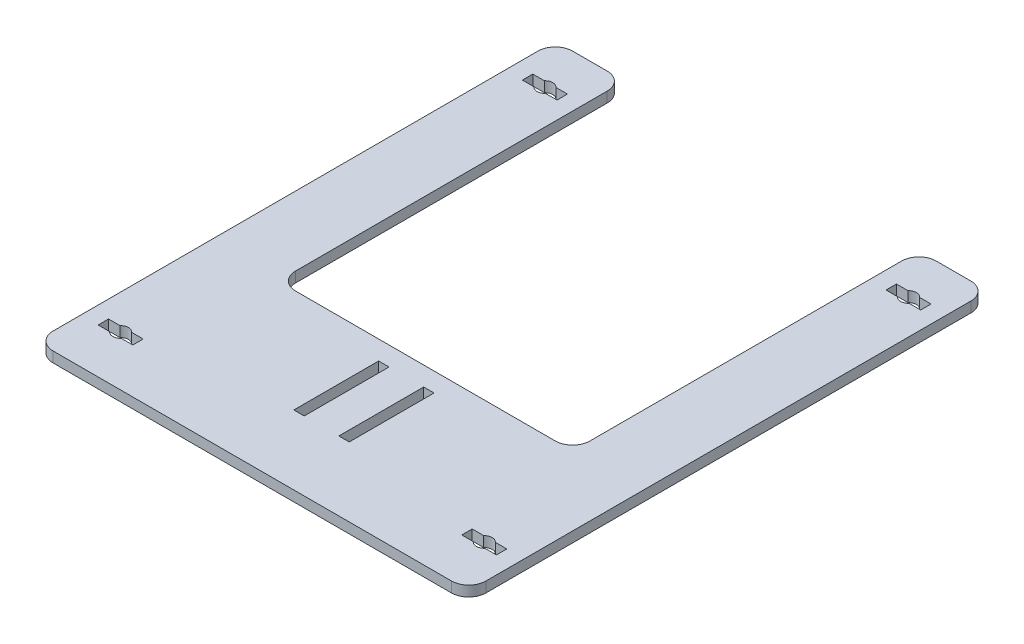
SolidWorks part; units mm, degrees
ref_plane "Front Plane" through (0, 0, 0) normal (0, 0, 1) x (1, 0, 0)
ref_plane "Top Plane" through (0, 0, 0) normal (0, 1, 0) x (1, 0, 0)
ref_plane "Right Plane" through (0, 0, 0) normal (1, 0, 0) x (0, 0, -1)
sketch "Sketch1" plane through (0, 0, 0) normal (0, 1, 0) x (1, 0, 0)
  line L0 (-164.1155, 87.3804) -> (-124.1155, 87.3804)
  line L1 (-124.1155, 87.3804) -> (-124.1155, -112.6196)
  line L2 (-124.1155, -112.6196) -> (45.8845, -112.6196)
  line L3 (45.8845, -112.6196) -> (45.8845, 87.3804)
  line L4 (45.8845, 87.3804) -> (85.8845, 87.3804)
  line L5 (85.8845, 87.3804) -> (85.8845, -212.6196)
  line L6 (85.8845, -212.6196) -> (-164.1155, -212.6196)
  line L7 (-164.1155, -212.6196) -> (-164.1155, 87.3804)
  dimension "D1" = 300
  dimension "D2" = 40
  dimension "D3" = 40
  dimension "D4" = 90
  dimension "D5" = 300
  dimension "D6" = 250
  dimension "D7" = 250
  dimension "D8" = 100
extrude "Boss-Extrude1" add sketch "Sketch1" along normal blind 6
fillet "Fillet1" radius 10 8 edges at (-164.1155, 3, -87.3804) (-124.1155, 3, -87.3804) (-124.1155, 3, 112.6196) (45.8845, 3, 112.6196) (45.8845, 3, -87.3804) (85.8845, 3, -87.3804) (85.8845, 3, 212.6196) (-164.1155, 3, 212.6196)
sketch "Sketch2" plane through (0, 0, 0) normal (0, -1, 0) x (1, 0, 0)
  line L0 (-55.1155, 172.6196) -> (-49.1155, 172.6196) construction
  line L1 (-29.1155, 172.6196) -> (-23.1155, 172.6196) construction
  line L2 (-55.1155, 172.6196) -> (-49.1155, 172.6196)
  line L3 (-29.1155, 172.6196) -> (-23.1155, 172.6196)
  line L4 (-55.1155, 172.6196) -> (-55.1155, 123.6196)
  line L5 (-55.1155, 123.6196) -> (-49.1155, 123.6196)
  line L6 (-49.1155, 277.6196) -> (-49.1155, -2.3804) construction
  line L7 (-49.1155, 123.6196) -> (-49.1155, 172.6196)
  line L8 (-164.1155, 202.6196) -> (-164.1155, -77.3804)
  line L9 (-154.1155, -87.3804) -> (-134.1155, -87.3804)
  line L10 (-124.1155, -77.3804) -> (-124.1155, 102.6196)
  line L11 (-114.1155, 112.6196) -> (35.8845, 112.6196)
  line L12 (45.8845, 102.6196) -> (45.8845, -77.3804)
  line L13 (55.8845, -87.3804) -> (75.8845, -87.3804)
  line L14 (85.8845, -77.3804) -> (85.8845, 202.6196)
  line L15 (75.8845, 212.6196) -> (-154.1155, 212.6196)
  line L16 (-164.1155, 202.6196) -> (-164.1155, -77.3804)
  line L17 (-154.1155, -87.3804) -> (-134.1155, -87.3804)
  line L18 (-124.1155, -77.3804) -> (-124.1155, 102.6196)
  line L19 (-114.1155, 112.6196) -> (35.8845, 112.6196)
  line L20 (45.8845, 102.6196) -> (45.8845, -77.3804)
  line L21 (55.8845, -87.3804) -> (75.8845, -87.3804)
  line L22 (85.8845, -77.3804) -> (85.8845, 202.6196)
  line L23 (75.8845, 212.6196) -> (-154.1155, 212.6196)
  line L24 (-29.1155, 172.6196) -> (-29.1155, 123.6196)
  line L25 (-29.1155, 123.6196) -> (-23.1155, 123.6196)
  line L26 (-23.1155, 277.6196) -> (-23.1155, -2.3804) construction
  line L27 (-23.1155, 123.6196) -> (-23.1155, 172.6196)
  arc A8 (-164.1155, -77.3804) -> (-154.1155, -87.3804) centre (-154.1155, -77.3804) ccw
  arc A9 (-134.1155, -87.3804) -> (-124.1155, -77.3804) centre (-134.1155, -77.3804) ccw
  arc A10 (-114.1155, 112.6196) -> (-124.1155, 102.6196) centre (-114.1155, 102.6196) ccw
  arc A11 (45.8845, 102.6196) -> (35.8845, 112.6196) centre (35.8845, 102.6196) ccw
  arc A12 (45.8845, -77.3804) -> (55.8845, -87.3804) centre (55.8845, -77.3804) ccw
  arc A13 (75.8845, -87.3804) -> (85.8845, -77.3804) centre (75.8845, -77.3804) ccw
  arc A14 (85.8845, 202.6196) -> (75.8845, 212.6196) centre (75.8845, 202.6196) ccw
  arc A15 (-154.1155, 212.6196) -> (-164.1155, 202.6196) centre (-154.1155, 202.6196) ccw
  arc A16 (-164.1155, -77.3804) -> (-154.1155, -87.3804) centre (-154.1155, -77.3804) ccw
  arc A17 (-134.1155, -87.3804) -> (-124.1155, -77.3804) centre (-134.1155, -77.3804) ccw
  arc A18 (-114.1155, 112.6196) -> (-124.1155, 102.6196) centre (-114.1155, 102.6196) ccw
  arc A19 (45.8845, 102.6196) -> (35.8845, 112.6196) centre (35.8845, 102.6196) ccw
  arc A20 (45.8845, -77.3804) -> (55.8845, -87.3804) centre (55.8845, -77.3804) ccw
  arc A21 (75.8845, -87.3804) -> (85.8845, -77.3804) centre (75.8845, -77.3804) ccw
  arc A22 (85.8845, 202.6196) -> (75.8845, 212.6196) centre (75.8845, 202.6196) ccw
  arc A23 (-154.1155, 212.6196) -> (-164.1155, 202.6196) centre (-154.1155, 202.6196) ccw
  dimension "D2" = 49
  dimension "D1" = 0
extrude "Cut-Extrude1" cut sketch "Sketch2" against normal through all flip side to cut
sketch "Sketch5" plane through (0, 0, 0) normal (0, -1, 0) x (-1, 0, 0)
  line L2 (164.1155, -81.977) -> (164.1155, 77.3804)
  line L3 (154.1155, 87.3804) -> (134.1155, 87.3804)
  line L4 (144.1155, 87.3804) -> (144.1155, 45.0532) construction
  line L5 (134.1155, 64.3804) -> (140.7614, 64.3804)
  line L6 (134.1155, 64.3804) -> (134.1155, 58.3804)
  line L7 (134.1155, 58.3804) -> (140.7614, 58.3804)
  line L8 (154.1155, 64.3804) -> (154.1155, 58.3804)
  line L9 (134.1155, 64.3804) -> (154.1155, 58.3804) construction
  line L10 (134.1155, 58.3804) -> (154.1155, 64.3804) construction
  line L11 (147.4696, 58.3804) -> (154.1155, 58.3804)
  line L12 (147.4696, 64.3804) -> (154.1155, 64.3804)
  line L13 (134.1155, 87.3804) -> (154.1155, 87.3804) construction
  line L14 (164.1155, 77.3804) -> (164.1155, -202.6196) construction
  line L15 (134.1155, 87.3804) -> (154.1155, 87.3804)
  line L16 (164.1155, 77.3804) -> (164.1155, -202.6196)
  arc A0 (147.4696, 64.3804) -> (140.7614, 64.3804) centre (144.1155, 61.3804) ccw
  arc A1 (140.7614, 58.3804) -> (147.4696, 58.3804) centre (144.1155, 61.3804) ccw
  point P4 (144.1155, 61.3804)
  dimension "D4" = 9
  dimension "D1" = 6
  dimension "D2" = 20
  dimension "D3" = 23
  dimension "D5" = 10
extrude "Cut-Extrude2" cut sketch "Sketch5" against normal through all contours L7 A1 L11 L8 L12 A0 L5 L6
pattern_linear "LPattern1" count 2 spacing 245 along (0, 0, 1) count 2 spacing 210 along (1, 0, 0) of "Cut-Extrude2"
equation "\"D3@Sketch1\"=\"D2@Sketch1\""
